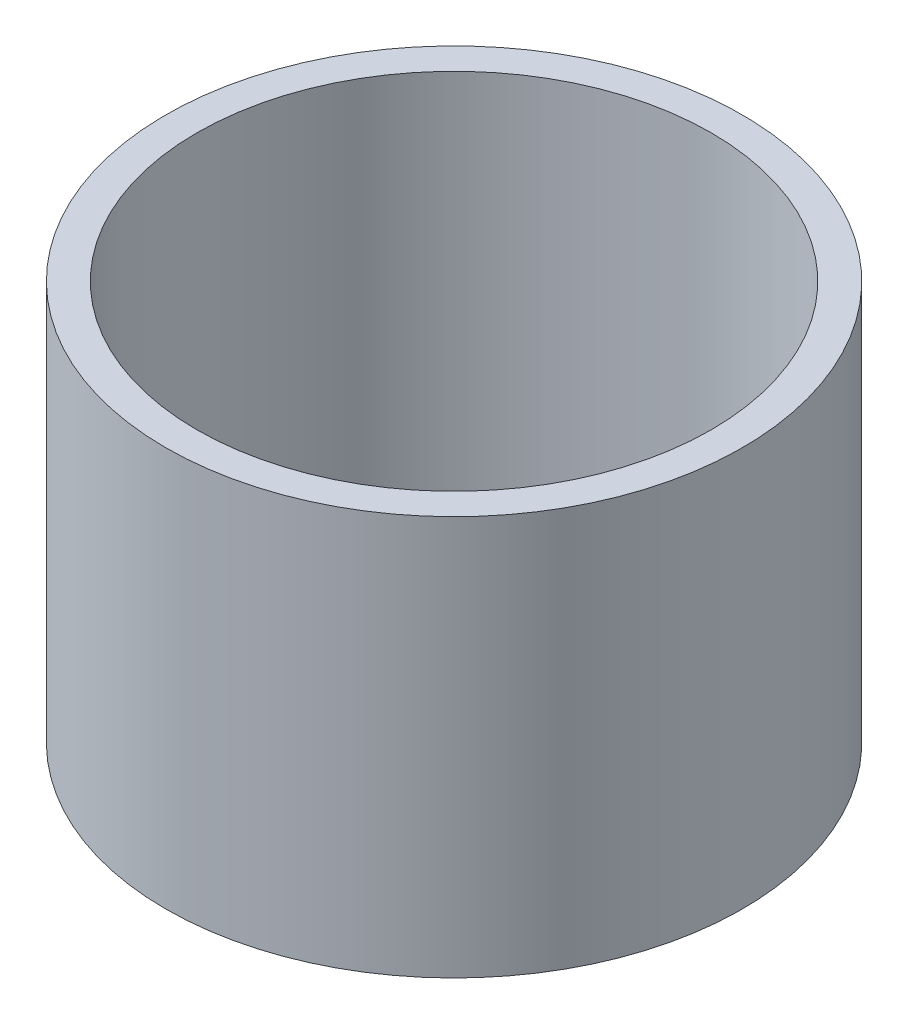
SolidWorks part; units mm, degrees
ref_plane "Front Plane" through (0, 0, 0) normal (0, 0, 1) x (1, 0, 0)
ref_plane "Top Plane" through (0, 0, 0) normal (0, 1, 0) x (1, 0, 0)
ref_plane "Right Plane" through (0, 0, 0) normal (1, 0, 0) x (0, 0, -1)
sketch "Sketch1" plane through (0, 0, 0) normal (0, 1, 0) x (1, 0, 0)
  circle A0 centre (0, 0) radius 31.75
  dimension "D1" = 63.5
extrude "Boss-Extrude1" add sketch "Sketch1" along normal blind 44
hole_wizard "G2 Tapped Hole1" positions "Sketch2" profile "Sketch3" tap size "G2" standard "DIN" end condition through all
sketch "Sketch2" plane through (0, 44, 0) normal (0, 1, 0) x (1, 0, 0)
  point P0 (0, 0)
sketch "Sketch3" plane through (0, 44, 0) normal (1, 0, 0) x (0, 0, 1)
  line L0 (0, 0) -> (0, 44)
  line L1 (0, 44) -> (28.328, 44)
  line L2 (28.328, 44) -> (28.328, 0)
  line L5 (28.328, 0) -> (0, 0)
  line L11 (0, -6.35) -> (0, 107.95) construction
  dimension "Thru Tap Drill Dia." = 56.656
  dimension "Thru Tap Drill Depth" = 44
cosmetic thread "Hole Thread1"
